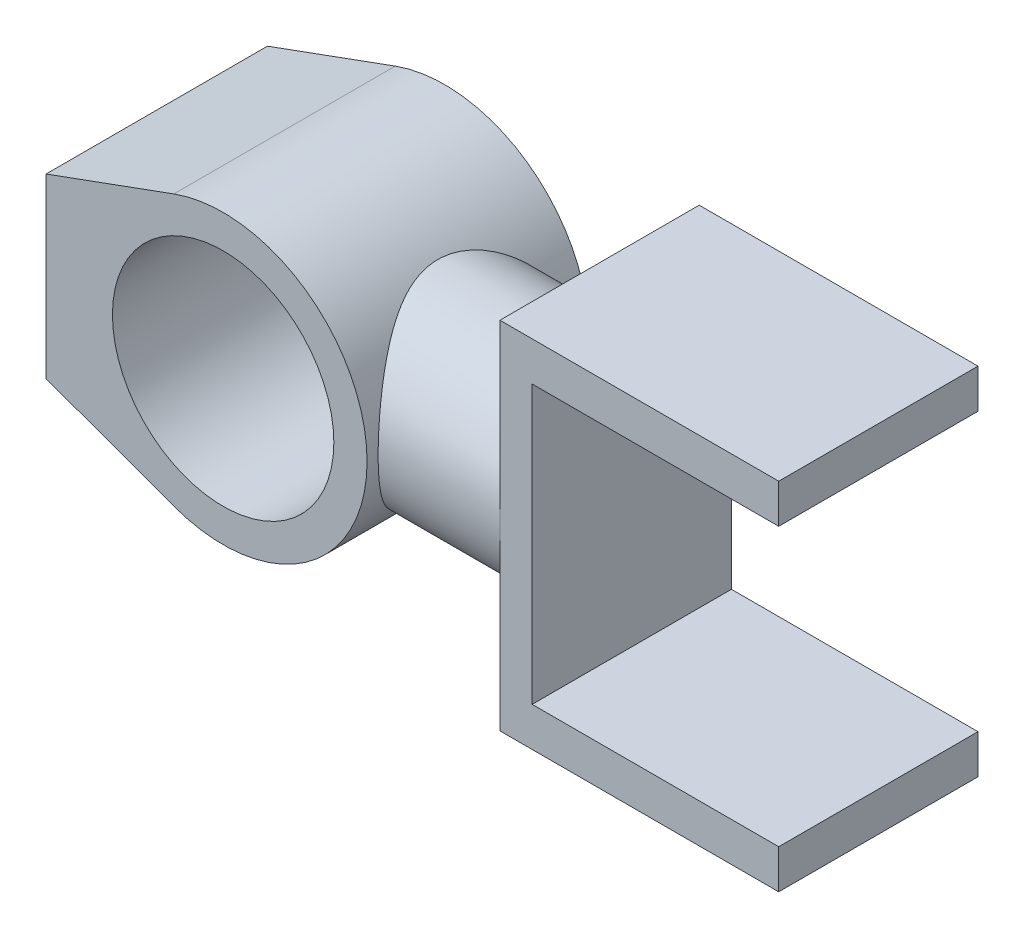
SolidWorks part; units mm, degrees
ref_plane "Front Plane" through (0, 0, 0) normal (0, 0, 1) x (1, 0, 0)
ref_plane "Top Plane" through (0, 0, 0) normal (0, 1, 0) x (1, 0, 0)
ref_plane "Right Plane" through (0, 0, 0) normal (1, 0, 0) x (0, 0, -1)
sketch "Sketch1" plane through (0, 0, 0) normal (0, 0, 1) x (1, 0, 0)
  line L0 (-80, 40) -> (-80, -40)
  line L1 (-80, 40) -> (-22.2817, 61.0617)
  line L2 (-80, -40) -> (-22.2817, -61.0617)
  arc A0 (-22.2817, -61.0617) -> (-22.2817, 61.0617) centre (0, 0) ccw
  circle A1 centre (0, 0) radius 50
  point P7 (-80, 0)
  dimension "D1" = 130
  dimension "D2" = 100
  dimension "D3" = 80
  dimension "D4" = 80
extrude "Boss-Extrude1" add sketch "Sketch1" along normal mid plane 100
ref_plane "Plane1" through (120, 0, 0) normal (1, 0, 0) x (0, 0, -1)
sketch "Sketch2" plane through (120, 0, 0) normal (1, 0, 0) x (0, 0, -1)
  circle A0 centre (0, 0) radius 45
  dimension "D1" = 90
extrude "Boss-Extrude2" add sketch "Sketch2" against normal up to next
sketch "Sketch3" plane through (0, 0, 0) normal (0, 0, 1) x (1, 0, 0)
  line L0 (120, 0) -> (238.0277, 0) construction
  line L11 (120, -45) -> (120, 45) construction
  line L12 (120, 45) -> (120, 80.3067)
  line L13 (120, 80.3067) -> (245.9038, 80.3067)
  line L14 (245.9038, 80.3067) -> (245.9038, 62.6533)
  line L15 (245.9038, 62.6533) -> (134.5503, 62.6533)
  line L16 (134.5503, 62.6533) -> (134.5503, -62.6533)
  line L17 (120, -80.3067) -> (245.9038, -80.3067)
  line L18 (120, -45) -> (120, -80.3067)
  line L19 (245.9038, -80.3067) -> (245.9038, -62.6533)
  line L20 (245.9038, -62.6533) -> (134.5503, -62.6533)
  line L21 (120, 45) -> (120, -45)
  point P18 (134.5503, 0)
extrude "Boss-Extrude3" add sketch "Sketch3" against normal blind 45 and the other way blind 45
